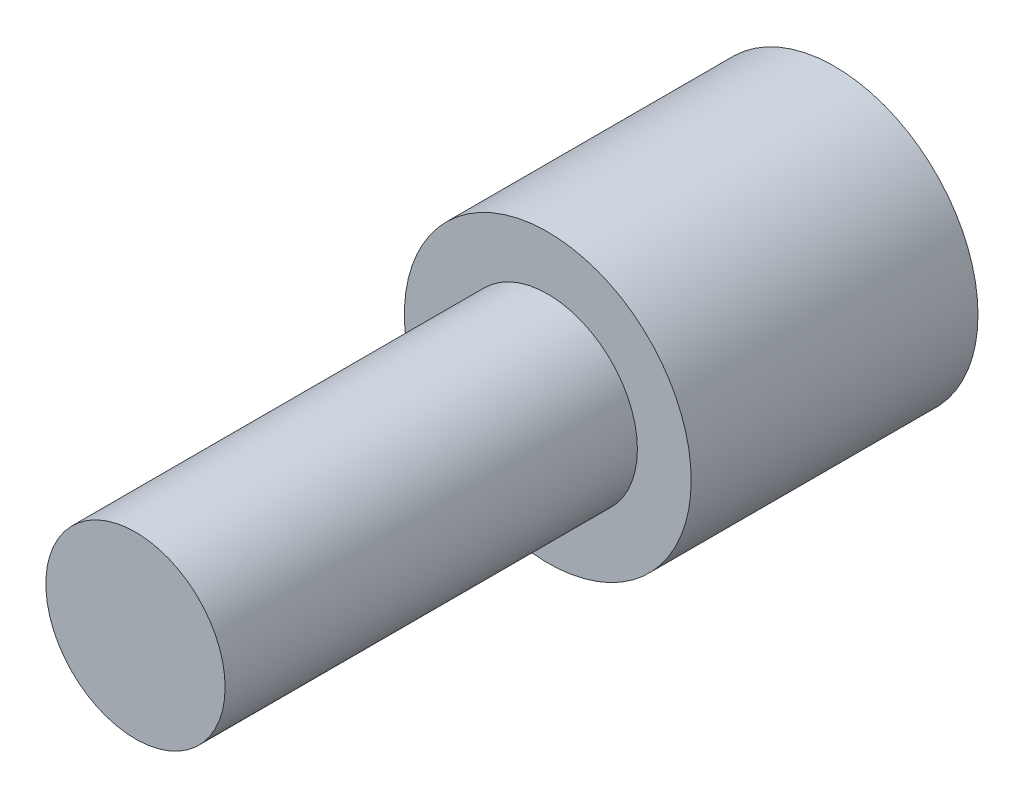
SolidWorks part; units mm, degrees
ref_plane "Front Plane" through (0, 0, 0) normal (0, 0, 1) x (1, 0, 0)
ref_plane "Top Plane" through (0, 0, 0) normal (0, 1, 0) x (1, 0, 0)
ref_plane "Right Plane" through (0, 0, 0) normal (1, 0, 0) x (0, 0, -1)
sketch "Sketch2" plane through (0, 0, 0) normal (0, 0, 1) x (1, 0, 0)
  circle A0 centre (0, 0) radius 20
  dimension "D1" = 40
extrude "Boss-Extrude1" add sketch "Sketch2" along normal blind 40
sketch "Sketch3" plane through (0, 0, 40) normal (0, 0, 1) x (1, 0, 0)
  circle A0 centre (0, 0) radius 12.5
extrude "Boss-Extrude2" add sketch "Sketch3" along normal blind 57.5
